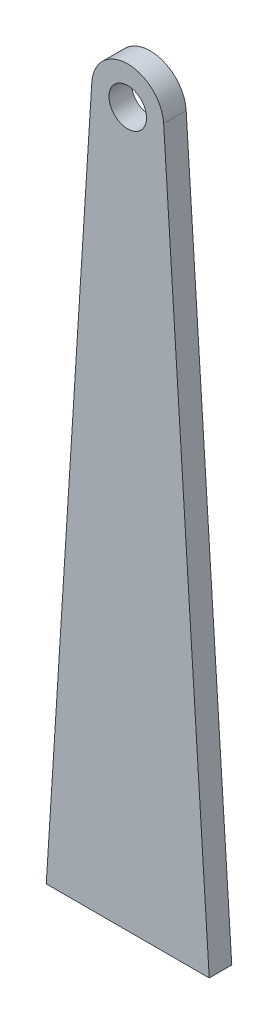
SolidWorks part; units mm, degrees
ref_plane "Спереди" through (0, 0, 0) normal (0, 0, 1) x (1, 0, 0)
ref_plane "Сверху" through (0, 0, 0) normal (0, 1, 0) x (1, 0, 0)
ref_plane "Справа" through (0, 0, 0) normal (1, 0, 0) x (0, 0, -1)
other "Configuration Table"
sketch "Sketch1" plane through (0, 0, 0) normal (0, 0, 1) x (1, 0, 0)
  line L0 (10.8536, -84.9058) -> (-10.8536, -84.9058)
  line L1 (-10.8536, -84.9058) -> (-4.7821, 10.6065)
  line L2 (0, -2.5384) -> (0, 6.0579) construction
  line L3 (10.8536, -84.9058) -> (4.7821, 10.6065)
  arc A0 (-4.7821, 10.6065) -> (0, 15.0942) centre (0, 10.3025) cw
  arc A1 (4.7821, 10.6065) -> (0, 15.0942) centre (0, 10.3025) ccw
  circle A2 centre (0, 10.0942) radius 2.5
  point P11 (0, -84.9058)
  dimension "D1" = 5
  dimension "D2" = 5
  dimension "D3" = 100
extrude "Boss-Extrude1" add sketch "Sketch1" along normal blind 3
